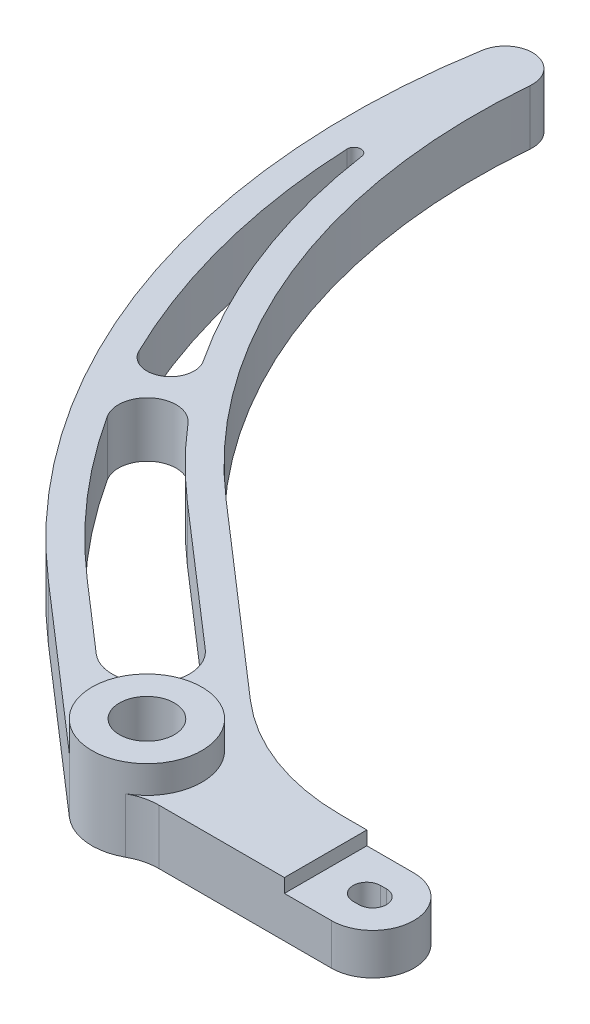
SolidWorks part; units mm, degrees
material "6061-T6 (SS)"
ref_plane "Front Plane" through (0, 0, 0) normal (0, 0, 1) x (1, 0, 0)
ref_plane "Top Plane" through (0, 0, 0) normal (0, 1, 0) x (1, 0, 0)
ref_plane "Right Plane" through (0, 0, 0) normal (1, 0, 0) x (0, 0, -1)
sketch "Sketch1" plane through (0, 0, 0) normal (0, 1, 0) x (1, 0, 0)
  line L0 (0, 0) -> (0, -165.1) construction
  line L1 (0, -165.1) -> (1.3399, -165.1) construction
  line L2 (0, -161.925) -> (1.3399, -161.925)
  line L3 (0, -168.275) -> (1.3399, -168.275)
  line L4 (1.3399, -174.625) -> (-42.3997, -174.625)
  line L5 (1.3399, -155.575) -> (-15.557, -155.575)
  line L6 (-91.9014, -105.7205) -> (-48.8848, -143.1142)
  line L7 (-59.1319, -174.6848) -> (-96.2538, -142.4153)
  line L8 (-50.8, -165.1) -> (0, -153.1955) construction
  line L9 (-139.5532, 12.1493) -> (-50.8, -165.1) construction
  line L10 (0, -165.1) -> (-50.8, -165.1) construction
  line L11 (-50.8, -165.1) -> (-177.6532, -12.7757) construction
  line L12 (-1.3399, -153.5095) -> (0, -153.5095) construction
  circle A0 centre (0, 0) radius 140.081 construction
  circle A1 centre (-50.8, -165.1) radius 6.35
  arc A2 (-139.5532, 12.1493) -> (-91.9014, -105.7205) centre (0, 0) ccw
  arc A3 (0, -161.925) -> (0, -168.275) centre (0, -165.1) ccw
  arc A4 (1.3399, -168.275) -> (1.3399, -161.925) centre (1.3399, -165.1) ccw
  arc A5 (1.3399, -155.575) -> (1.3399, -174.625) centre (1.3399, -165.1) cw
  arc A6 (-42.3997, -174.625) -> (-59.1319, -174.6848) centre (-50.8, -165.1) cw
  arc A7 (-15.557, -155.575) -> (-48.8848, -143.1142) centre (-15.557, -104.775) cw
  arc A8 (-96.2538, -142.4153) -> (-152.1399, 13.7613) centre (14.8935, -14.555) cw
  arc A9 (-152.1399, 13.7613) -> (-139.5532, 12.1493) centre (-145.8792, 12.7) cw
  circle A10 centre (-50.8, -165.1) radius 50.8 construction
  arc A11 (-67.0543, -145.5819) -> (-62.1724, -142.3881) centre (-50.8, -165.1) cw construction
  arc A12 (-25.4, -165.1) -> (-26.07, -159.3048) centre (-50.8, -165.1) ccw construction
  circle A13 centre (-1.3399, -153.5095) radius 9.525 construction
  point P0 (0.67, -165.1)
  point P19 (0, 0)
  point P34 (-37.2801, -153.1955)
  point P35 (-31.8532, -155.575)
  point P36 (-43.9416, -154.8681)
  point P40 (-39.2783, -150.7815)
  point P41 (-37.7059, -152.7729)
  point P42 (-50.8, -165.1)
  point P43 (-47.287, -163.0249)
  dimension "D1" = 280.162
  dimension "D2" = 50.8
  dimension "D4" = 3.175
  dimension "D5" = 9.525
  dimension "D6" = 6.35
  dimension "D7" = 12.7
  dimension "D9" = 6.35
  dimension "D11" = 25.4
  dimension "D3" = 101.6
  dimension "D8" = 49
  dimension "D10" = 38.1
  dimension "D12" = 165.1
  dimension "D13" = 12.7
extrude "Boss-Extrude1" add sketch "Sketch1" along normal blind 12.7
sketch "Sketch3" plane through (0, 12.7, 0) normal (0, 1, 0) x (1, 0, 0)
  line L0 (-126.7212, -83.7361) -> (-116.6134, -99.2045) construction
  line L1 (-50.8, -165.1) -> (-70.134, -144.8817) construction
  line L2 (-53.0508, -147.9067) -> (-96.0674, -110.5129)
  line L3 (-64.2789, -138.1462) -> (-96.0674, -110.5129)
  line L4 (-146.4309, -21.6211) -> (-126.7212, -83.7361) construction
  line L5 (-92.0878, -137.6229) -> (-54.966, -169.8924)
  line L6 (-92.0878, -137.6229) -> (-75.9891, -151.6173)
  line L7 (-116.6134, -99.2045) -> (-70.134, -144.8817) construction
  arc A0 (-122.1683, -80.7276) -> (-131.6245, -86.1314) centre (-126.7212, -83.7361) cw
  arc A1 (-122.2227, -102.8151) -> (-111.5323, -94.8819) centre (-116.6134, -99.2045) cw
  arc A2 (-122.2227, -102.8151) -> (-92.0878, -137.6229) centre (14.8935, -14.555) ccw
  arc A3 (-148.0169, -21.6906) -> (-144.8604, -21.3892) centre (-146.4309, -21.6211) cw
  arc A4 (-111.5323, -94.8819) -> (-96.0674, -110.5129) centre (0, 0) ccw
  arc A5 (-145.8792, 12.7) -> (-92.0878, -137.6229) centre (14.8935, -14.555) ccw
  arc A6 (-145.8792, 12.7) -> (-96.0674, -110.5129) centre (0, 0) ccw
  arc A7 (-144.8604, -21.3892) -> (-122.1683, -80.7276) centre (0, 0) ccw
  arc A8 (-148.0169, -21.6906) -> (-131.6245, -86.1314) centre (14.8935, -14.555) ccw
  arc A9 (-64.2789, -138.1462) -> (-75.9891, -151.6173) centre (-70.134, -144.8817) cw
  circle A10 centre (-50.8, -165.1) radius 6.35 construction
  point P16 (-123.7361, -88.3043)
  point P17 (-120.2625, -93.6201)
  point P21 (-63.9659, -151.3319)
  point P22 (-55.1886, -160.5106)
  dimension "D3" = 1.5875
  dimension "D4" = 6.35
  dimension "D5" = 12.7
  dimension "D1" = 6.35
  dimension "D2" = 6.35
extrude "Cut-Extrude2" cut sketch "Sketch3" against normal through all
fillet "Fillet1" radius 12.7 1 edges at (-42.3997, 6.35, 174.625)
sketch "Sketch4" plane through (0, 12.7, 0) normal (0, 1, 0) x (1, 0, 0)
  circle A0 centre (-50.8, -165.1) radius 12.7
  circle A1 centre (-50.8, -165.1) radius 6.35 construction
  circle A2 centre (-50.8, -165.1) radius 6.35
extrude "Boss-Extrude2" add sketch "Sketch4" along normal blind 6.35
sketch "Sketch2" plane through (0, 12.7, 0) normal (0, 1, 0) x (1, 0, 0)
  line L0 (1.3399, -155.575) -> (-15.557, -155.575) construction
  line L3 (-9.525, -150.4585) -> (17.5489, -150.4585)
  line L4 (-9.525, -150.4585) -> (-9.525, -180.0553)
  line L5 (-9.525, -180.0553) -> (17.5489, -180.0553)
  line L6 (17.5489, -150.4585) -> (17.5489, -180.0553)
  circle A0 centre (0, -165.1) radius 9.525 construction
extrude "Cut-Extrude1" cut sketch "Sketch2" against normal blind 3.175
